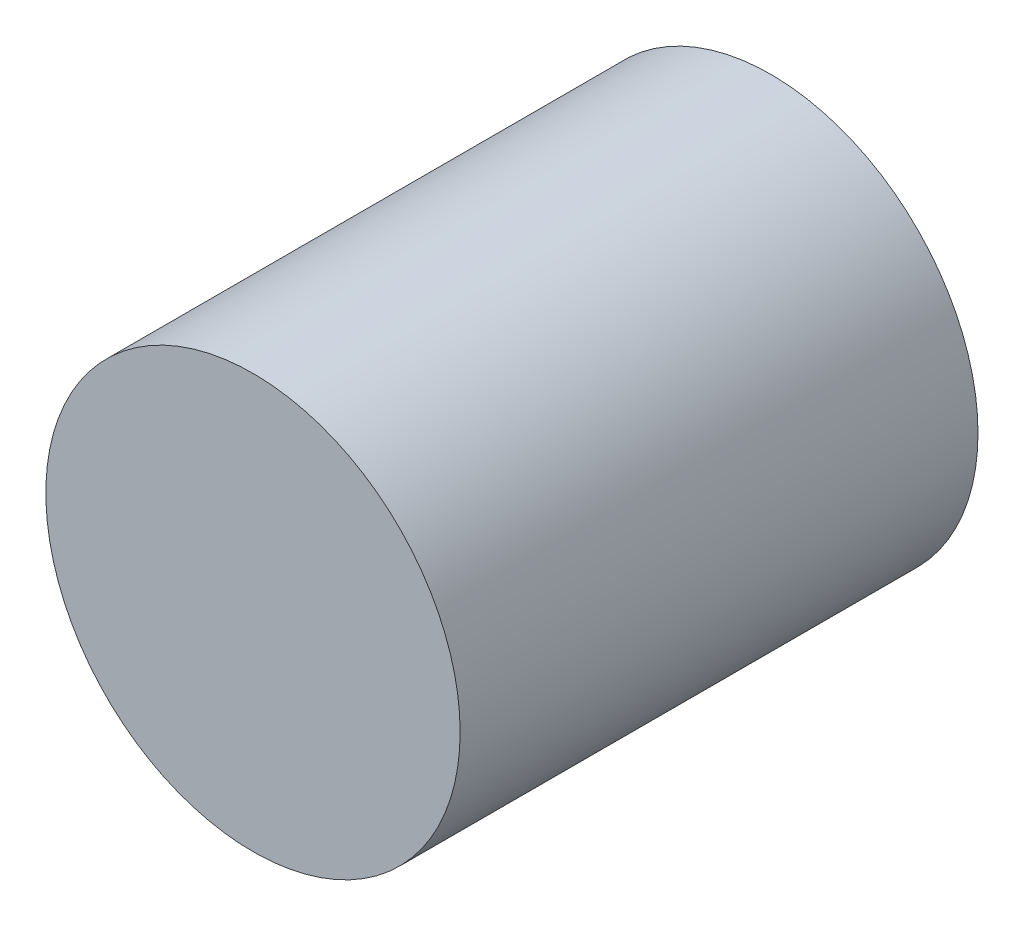
SolidWorks part; units mm, degrees
ref_plane "Alzado" through (0, 0, 0) normal (0, 0, 1) x (1, 0, 0)
ref_plane "Planta" through (0, 0, 0) normal (0, 1, 0) x (1, 0, 0)
ref_plane "Vista lateral" through (0, 0, 0) normal (1, 0, 0) x (0, 0, -1)
sketch "Croquis1" plane through (0, 0, 0) normal (0, 0, 1) x (1, 0, 0)
  circle A0 centre (0, 0) radius 294
  dimension "D1" = 588
extrude "Saliente-Extruir2" add sketch "Croquis1" along normal blind 735
